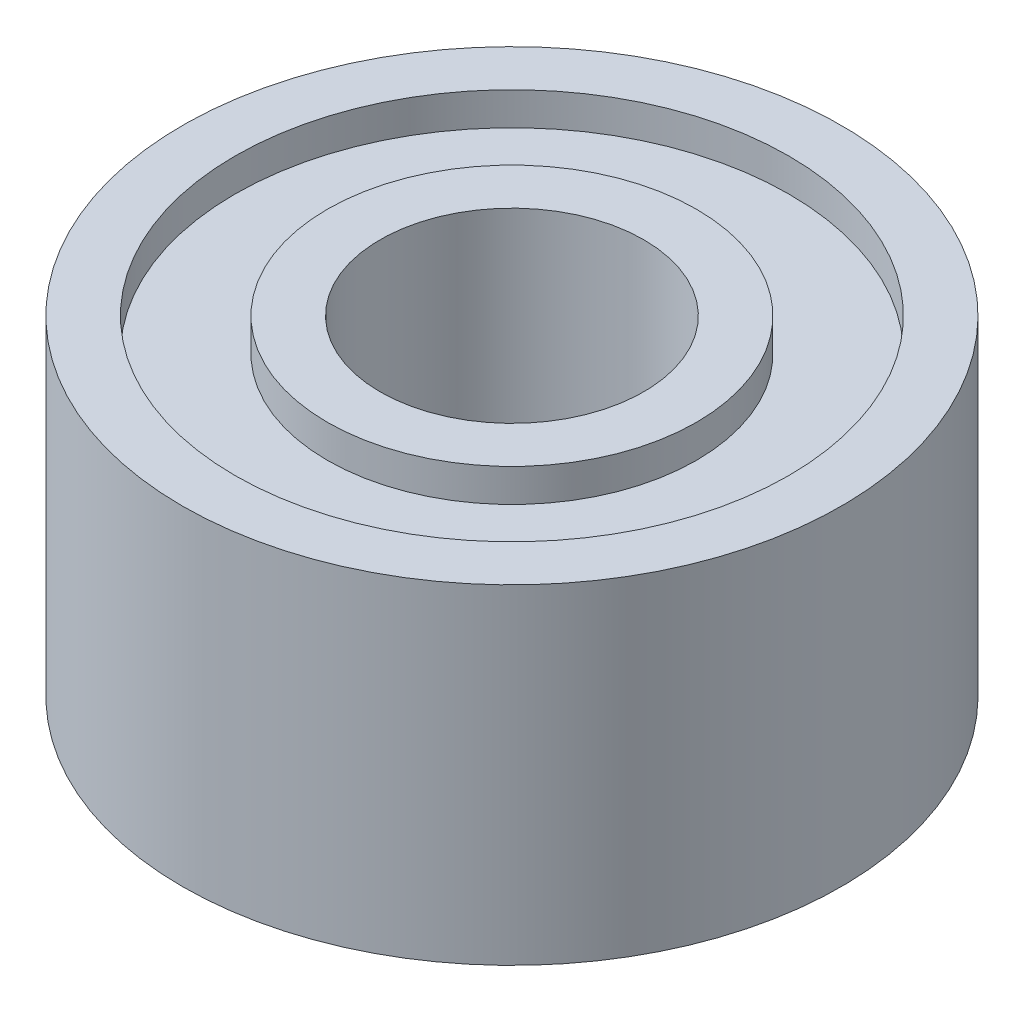
SolidWorks part; units mm, degrees
ref_plane "Front Plane" through (0, 0, 0) normal (0, 0, 1) x (1, 0, 0)
ref_plane "Top Plane" through (0, 0, 0) normal (0, 1, 0) x (1, 0, 0)
ref_plane "Right Plane" through (0, 0, 0) normal (1, 0, 0) x (0, 0, -1)
sketch "Sketch1" plane through (0, 0, 0) normal (0, 1, 0) x (1, 0, 0)
  circle A0 centre (0, 0) radius 2.5
  circle A1 centre (0, 0) radius 1
  dimension "D1" = 2
  dimension "D2" = 5
extrude "Boss-Extrude1" add sketch "Sketch1" along normal mid plane 2.5
sketch "Sketch2" plane through (0, 1.25, 0) normal (0, 1, 0) x (1, 0, 0)
  circle A2 centre (0, 0) radius 2.1
  circle A3 centre (0, 0) radius 2.1
  circle A5 centre (0, 0) radius 1.4
  circle A6 centre (0, 0) radius 1.4
  dimension "D1" = 0.4
  dimension "D2" = 0.4
extrude "Cut-Extrude1" cut sketch "Sketch2" against normal blind 0.25
mirror "Mirror1" about plane through (0, 0, 0) normal (0, 1, 0) of "Cut-Extrude1"
